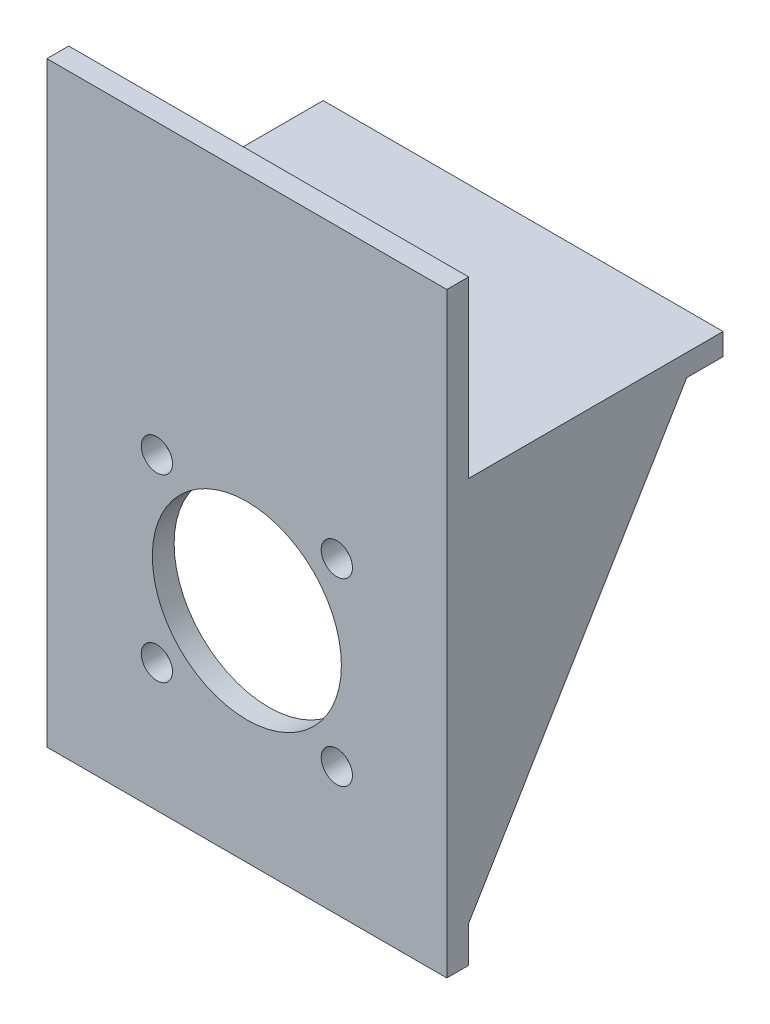
SolidWorks part; units mm, degrees
ref_plane "Front Plane" through (0, 0, 0) normal (0, 0, 1) x (1, 0, 0)
ref_plane "Top Plane" through (0, 0, 0) normal (0, 1, 0) x (1, 0, 0)
ref_plane "Right Plane" through (0, 0, 0) normal (1, 0, 0) x (0, 0, -1)
sketch "Sketch1" plane through (0, 0, 0) normal (0, 1, 0) x (1, 0, 0)
  line L0 (-27.5, 17.5) -> (27.5, -17.5) construction
  line L1 (-27.5, 17.5) -> (27.5, 17.5)
  line L2 (-27.5, 17.5) -> (-27.5, -17.5)
  line L3 (-27.5, -17.5) -> (27.5, -17.5)
  line L4 (27.5, 17.5) -> (27.5, -17.5)
  dimension "D1" = 55
  dimension "D2" = 35
extrude "Boss-Extrude1" add sketch "Sketch1" along normal blind 3
sketch "Sketch2" plane through (0, 0, 17.5) normal (0, 0, 1) x (1, 0, 0)
  line L1 (-27.5, 27) -> (27.5, 27)
  line L2 (-27.5, 27) -> (-27.5, -55)
  line L3 (-27.5, -55) -> (27.5, -55)
  line L4 (27.5, 27) -> (27.5, -55)
  line L5 (-27.5, 3) -> (-27.5, 0) construction
  line L6 (-27.5, 3) -> (27.5, 3) construction
  line L7 (-27.5, 0) -> (27.5, 0) construction
  dimension "D1" = 24
  dimension "D2" = 55
extrude "Boss-Extrude2" add sketch "Sketch2" along normal blind 3
sketch "Sketch3" plane through (27.5, 0, 0) normal (1, 0, 0) x (0, 0, -1)
  line L0 (-17.5, 0) -> (12.5, 0)
  line L1 (-17.5, 0) -> (17.5, 0) construction
  line L2 (12.5, 0) -> (-17.5, -50)
  line L3 (-17.5, -55) -> (-17.5, 0) construction
  line L4 (-17.5, -50) -> (-17.5, 0)
  dimension "D1" = 50
  dimension "D2" = 30
extrude "Boss-Extrude3" add sketch "Sketch3" against normal blind 3
sketch "Sketch4" plane through (-27.5, 0, 0) normal (-1, 0, 0) x (0, 0, 1)
  line L0 (-12.5, 0) -> (17.5, 0)
  line L1 (17.5, 0) -> (17.5, -50)
  line L2 (17.5, -50) -> (-12.5, 0)
extrude "Boss-Extrude4" add sketch "Sketch4" against normal blind 3
sketch "Sketch5" plane through (0, 0, 17.5) normal (0, 0, -1) x (-1, 0, 0)
  line L0 (-24.5, 0) -> (24.5, -55) construction
  line L1 (27.5, -55) -> (-27.5, -55) construction
  line L2 (0, 0) -> (0, -25) construction
  line L3 (0, -25) -> (12.3744, -12.6256) construction
  circle A0 centre (0, -25) radius 13
  circle A1 centre (0, -25) radius 17.5 construction
  circle A2 centre (12.3744, -12.6256) radius 2.15
  circle A3 centre (12.3744, -37.3744) radius 2.15
  circle A4 centre (-12.3744, -37.3744) radius 2.15
  circle A5 centre (-12.3744, -12.6256) radius 2.15
  point P21 (0, -25)
  dimension "D2" = 26
  dimension "D3" = 35
  dimension "D4" = 45
  dimension "D5" = 4.3
  dimension "D1" = 25
  dimension "D6" = 4
extrude "Cut-Extrude1" cut sketch "Sketch5" against normal blind 3
